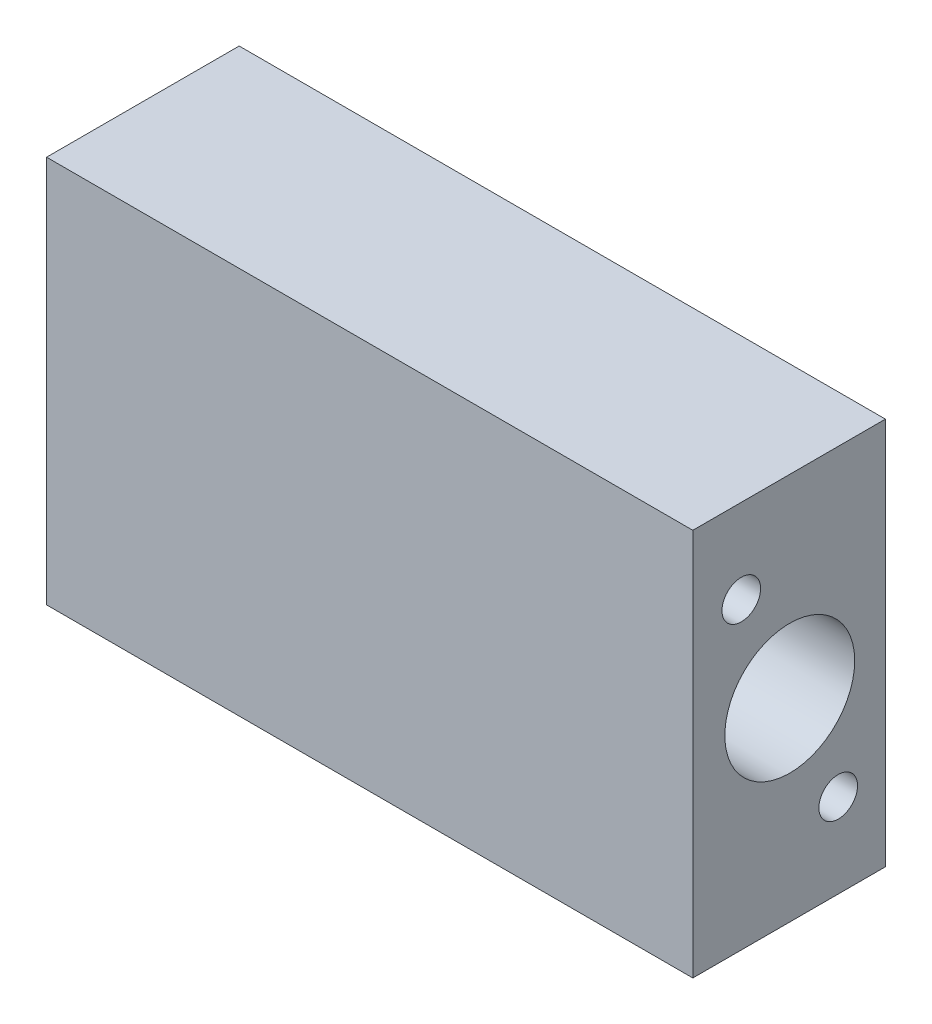
SolidWorks part; units mm, degrees
material "6061-T6 (SS)"
ref_plane "Front Plane" through (0, 0, 0) normal (0, 0, 1) x (1, 0, 0)
ref_plane "Top Plane" through (0, 0, 0) normal (0, 1, 0) x (1, 0, 0)
ref_plane "Right Plane" through (0, 0, 0) normal (1, 0, 0) x (0, 0, -1)
sketch "Sketch1" plane through (0, 0, 0) normal (0, 0, 1) x (1, 0, 0)
  line L0 (11.4863, 17.9021) -> (11.4863, 30.6021) construction
  line L5 (11.4863, 30.6021) -> (25.7738, 30.6021) construction
  line L6 (-37.7262, 43.3021) -> (25.7738, 43.3021)
  line L7 (-37.7262, 43.3021) -> (-37.7262, 5.2021)
  line L8 (-37.7262, 5.2021) -> (25.7738, 5.2021)
  line L9 (25.7738, 43.3021) -> (25.7738, 5.2021)
  line L10 (-31.3708, 30.6021) -> (-31.3708, 17.9021) construction
  line L12 (-47.0828, 17.9021) -> (16.4172, 17.9021) construction
  line L14 (-58.7813, 30.6021) -> (4.7187, 30.6021) construction
  line L15 (-31.3708, 17.9021) -> (-35.1862, 24.2521) construction
  line L16 (-35.1862, 24.2521) -> (-31.3708, 30.6021) construction
  line L17 (25.7738, 30.6021) -> (25.7738, 32.1896)
  line L18 (25.7738, 32.1896) -> (27.3613, 32.1896) construction
  line L19 (27.3613, 32.1896) -> (27.3613, 16.3146) construction
  line L20 (27.3613, 16.3146) -> (25.7738, 16.3146) construction
  line L21 (25.7738, 16.3146) -> (25.7738, 17.9021)
  line L22 (25.7738, 17.9021) -> (11.4863, 17.9021) construction
  line L26 (-984.125, 24.2521) -> (49015.875, 24.2521) construction
  circle A0 centre (52.7613, 24.2521) radius 25.4 construction
  point P9 (25.7738, 24.2521)
  point P13 (-37.7262, 24.2521)
  dimension "D2" = 26.9875
  dimension "D3" = 38.1
  dimension "D4" = 12.7
  dimension "D5" = 118
  dimension "D6" = 2.54
  dimension "D7" = 63.5
  dimension "D8" = 15.875
  dimension "D10" = 15.875
  dimension "D11" = 1.5875
extrude "Boss-Extrude1" add sketch "Sketch1" along normal blind 19.05 contours L7 L6 L9 L8
hole_wizard "1/2 (0.5025) Diameter Hole1" positions "Sketch2" profile "Sketch3" hole size "1/2" standard "ANSI Inch"
sketch "Sketch2" plane through (25.7738, 0, 0) normal (1, 0, 0) x (0, 0, -1)
  line L0 (-9.525, 24.2521) -> (-19.05, 24.2521) construction
  line L1 (-19.05, 5.2021) -> (-19.05, 43.3021) construction
  point P0 (-9.525, 24.2521)
  dimension "D1" = 9.525
sketch "Sketch3" plane through (25.7738, 24.2521, 9.525) normal (0, 1, 0) x (0, 0, -1)
  line L0 (0, 0) -> (0, 60.9791)
  line L1 (0, 60.9791) -> (6.3817, 57.1445)
  line L2 (6.3817, 57.1445) -> (6.3817, 0)
  line L5 (6.3817, 0) -> (0, 0)
  line L10 (0, 60.9791) -> (-6.3818, 57.1445) construction
  line L11 (0, -6.35) -> (0, 107.95) construction
  dimension "Hole Dia." = 12.7635
  dimension "Hole Depth" = 57.1445
  dimension "Drill Angle" = 118
sketch "Sketch9" plane through (0, 0, 0) normal (0, 0, -1) x (-1, 0, 0)
  line L0 (37.7262, 43.3021) -> (37.7262, 5.2021) construction
  line L1 (37.7262, 43.3021) -> (-25.7738, 43.3021) construction
  circle A0 centre (10.7387, 24.2521) radius 4.7498
  dimension "D1" = 9.4996
  dimension "D2" = 26.9875
  dimension "D3" = 19.05
hole_wizard "#35 (0.11) Diameter Hole1" positions "Sketch6" profile "Sketch8" hole size "#35" standard "ANSI Inch"
sketch "Sketch6" plane through (0, 0, 0) normal (0, 0, -1) x (-1, 0, 0)
  line L11 (-25.7738, 24.2521) -> (37.7262, 24.2521) construction
  line L12 (-25.7738, 43.3021) -> (-25.7738, 5.2021) construction
  line L13 (37.7262, 43.3021) -> (37.7262, 5.2021) construction
  line L16 (-4.5953, 20.1434) -> (26.0728, 28.3609) construction
  line L18 (-4.5953, 28.3609) -> (26.0728, 20.1434) construction
  circle A6 centre (10.7387, 24.2521) radius 15.875 construction
  circle A7 centre (10.7387, 24.2521) radius 25.4 construction
  point P59 (26.2501, 20.8739)
  point P62 (26.2501, 27.6303)
  point P80 (-14.4356, 27.6303)
  point P82 (-14.4356, 20.8739)
  point P118 (10.7387, 24.2521)
  dimension "D1" = 31.75
  dimension "D2" = 50.8
  dimension "D3" = 26.9875
  dimension "D4" = 15
  dimension "D5" = 15
  dimension "D6" = 3.3782
sketch "Sketch8" plane through (-26.2501, 20.8739, 0) normal (1, 0, 0) x (0, 1, 0)
  line L0 (0, 0) -> (0, 10.4914)
  line L1 (0, 10.4914) -> (1.397, 9.652)
  line L2 (1.397, 9.652) -> (1.397, 0)
  line L5 (1.397, 0) -> (0, 0)
  line L10 (0, 10.4914) -> (-1.397, 9.652) construction
  line L11 (0, -6.35) -> (0, 107.95) construction
  dimension "Hole Dia." = 2.794
  dimension "Hole Depth" = 9.652
  dimension "Drill Angle" = 118
hole_wizard "#10-24 Tapped Hole1" positions "Sketch12" profile "Sketch14" tap size "#10-24" standard "ANSI Inch"
sketch "Sketch12" plane through (25.7738, 0, 0) normal (1, 0, 0) x (0, 0, -1)
  line L0 (-1000, 24.2521) -> (49000, 24.2521) construction
  line L1 (-9.525, 24.2521) -> (-13.0552, 32.2379) construction
  line L2 (-13.0552, 32.2379) -> (-14.2875, 35.0257) construction
  line L3 (-9.525, 24.2521) -> (-5.9948, 16.2663) construction
  line L5 (-5.9948, 16.2663) -> (-4.7625, 13.4786) construction
  line L6 (-19.05, 43.3021) -> (-19.05, 5.2021) construction
  circle A1 centre (-9.525, 24.2521) radius 6.3817 construction
  circle A2 centre (-9.525, 24.2521) radius 8.7312 construction
  point P0 (-4.7625, 13.4786)
  point P2 (-14.2875, 35.0257)
  dimension "D3" = 17.4625
  dimension "D1" = 3.048
  dimension "D4" = 4.7625
  dimension "D2" = 4.7625
cosmetic thread "Hole Thread2" parameters "D1"=6.35, "D2"=4.826
sketch "Sketch14" plane through (25.7738, 13.4786, 4.7625) normal (0, 1, 0) x (0, 0, -1)
  line L0 (0, 0) -> (0, 11.176)
  line L1 (0, 11.176) -> (1.8986, 10.0352)
  line L2 (1.8986, 10.0352) -> (1.8986, 0)
  line L5 (1.8986, 0) -> (0, 0)
  line L10 (0, 11.176) -> (-1.8987, 10.0352) construction
  line L11 (0, -6.35) -> (0, 107.95) construction
  dimension "Tap Drill Dia." = 3.7973
  dimension "Tap Drill Depth" = 11.176
  dimension "Drill Angle" = 118
cosmetic thread "Hole Thread3" parameters "D1"=6.35, "D2"=4.826
extrude "Boss-Extrude2" add sketch "Sketch9" along normal blind 6.35
hole_wizard "#10-24 Tapped Hole2" positions "Sketch15" profile "Sketch17" tap size "#10-24" standard "ANSI Inch"
sketch "Sketch15" plane through (0, 0, -6.35) normal (0, 0, -1) x (-1, 0, 0)
  circle A0 centre (10.7387, 24.2521) radius 4.7498 construction
  point P0 (10.7387, 24.2521)
sketch "Sketch17" plane through (-10.7387, 24.2521, -6.35) normal (1, 0, 0) x (0, 1, 0)
  line L0 (0, 0) -> (0, 11.5548)
  line L1 (0, 11.5548) -> (1.8986, 10.414)
  line L2 (1.8986, 10.414) -> (1.8986, 0.6414)
  line L3 (1.8986, 0.6414) -> (2.54, 0)
  line L5 (2.54, 0) -> (0, 0)
  line L6 (-1.8986, 0.6414) -> (-2.54, 0) construction
  line L10 (0, 11.5548) -> (-1.8987, 10.414) construction
  line L11 (0, -6.35) -> (0, 107.95) construction
  dimension "Tap Drill Dia." = 3.7973
  dimension "Tap Drill Depth" = 10.414
  dimension "Near C'Sink Dia." = 5.08
  dimension "Near C'Sink Angle" = 90
  dimension "Drill Angle" = 118
cosmetic thread "Hole Thread4" parameters "D1"=5.08, "D2"=4.826
chamfer "Chamfer1" distance 0.127 angle 45 9 edges at (-5.9762, 43.3021, 0) (25.7738, 24.2521, 0) (-5.9762, 5.2021, 0) (-37.7262, 24.2521, 0) (-15.4885, 24.2521, -6.35) (13.0386, 20.8739, 0) (13.0386, 27.6303, 0) (-27.6471, 20.8739, 0) (-27.6471, 27.6303, 0)
equation "\"D1@Sketch9\"=3/8-.001"
equation "\"D2@Sketch12\"=(0.361+0.014)/2"
